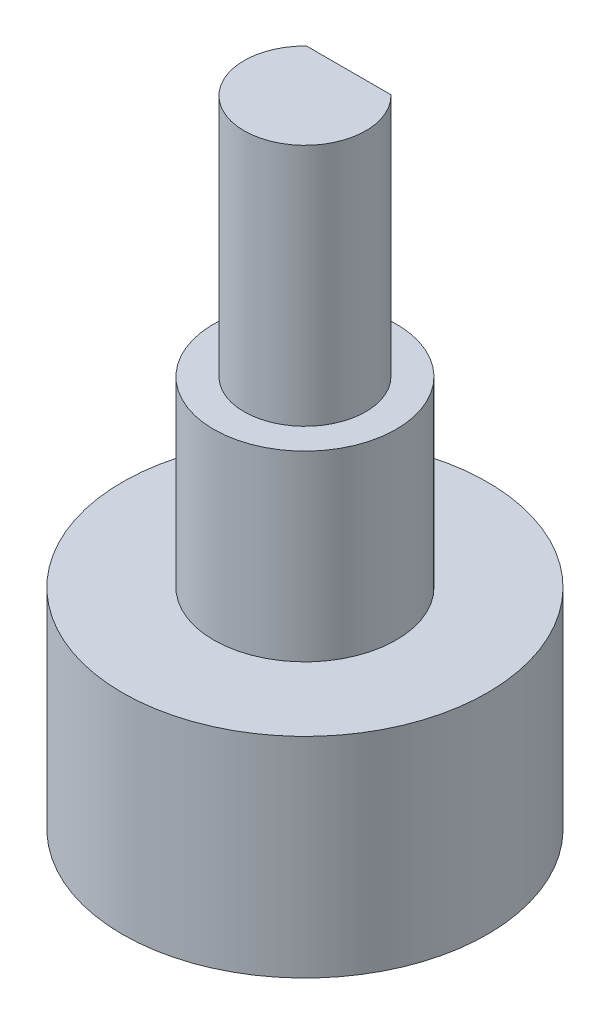
SolidWorks part; units mm, degrees
ref_plane "Front Plane" through (0, 0, 0) normal (0, 0, 1) x (1, 0, 0)
ref_plane "Top Plane" through (0, 0, 0) normal (0, 1, 0) x (1, 0, 0)
ref_plane "Right Plane" through (0, 0, 0) normal (1, 0, 0) x (0, 0, -1)
sketch "Sketch1" plane through (0, 0, 0) normal (0, 1, 0) x (1, 0, 0)
  circle A0 centre (0, 0) radius 9.525
extrude "Boss-Extrude1" add sketch "Sketch1" along normal blind 10.922
sketch "Sketch2" plane through (0, 10.922, 0) normal (0, 1, 0) x (1, 0, 0)
  circle A0 centre (0, 0) radius 4.7625
  dimension "D1" = 9.525
extrude "Boss-Extrude2" add sketch "Sketch2" along normal blind 9.525
sketch "Sketch3" plane through (0, 20.447, 0) normal (0, 1, 0) x (1, 0, 0)
  line L0 (-2.2034, 2.286) -> (2.2034, 2.286)
  arc A0 (-2.2034, 2.286) -> (2.2034, 2.286) centre (0, 0) ccw
  dimension "D1" = 2.286
  dimension "D2" = 6.35
extrude "Boss-Extrude3" add sketch "Sketch3" along normal blind 12.7
